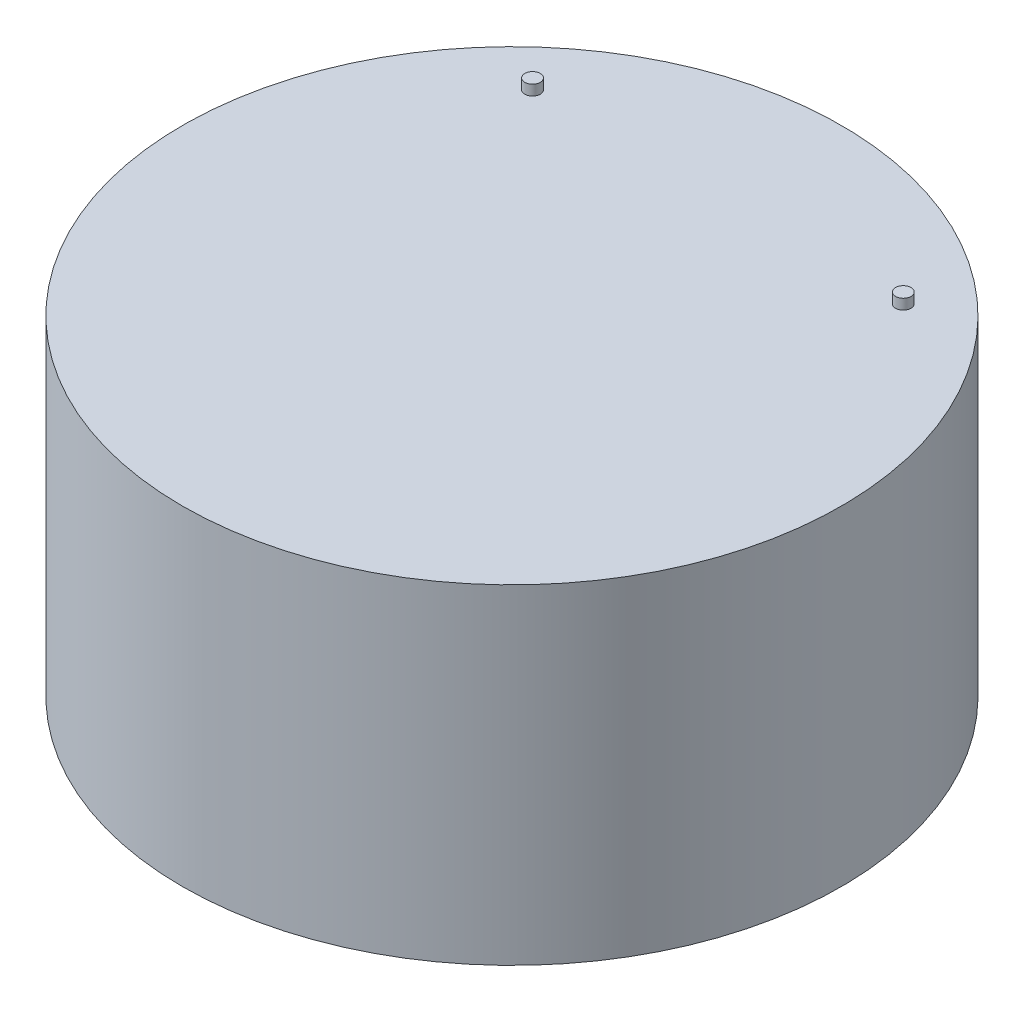
SolidWorks part; units mm, degrees
ref_plane "Front" through (0, 0, 0) normal (0, 0, 1) x (1, 0, 0)
ref_plane "Top" through (0, 0, 0) normal (0, 1, 0) x (1, 0, 0)
ref_plane "Right" through (0, 0, 0) normal (1, 0, 0) x (0, 0, -1)
sketch "Sketch1" plane through (0, 0, 0) normal (0, 1, 0) x (1, 0, 0)
  circle A0 centre (0, 0) radius 50.8
  dimension "D1" = 101.6
extrude "Boss-Extrude1" add sketch "Sketch1" along normal blind 50.8
sketch "Sketch3" plane through (0, 50.8, 0) normal (0, 1, 0) x (1, 0, 0)
  line L0 (0, 50.8) -> (0, -50.8) construction
  line L1 (28.575, 31.75) -> (39.6557, 31.75) construction
  line L2 (39.6557, 31.75) -> (-39.6557, 31.75) construction
  circle A0 centre (0, 0) radius 50.8 construction
  circle A1 centre (28.575, 31.75) radius 1.1906
  circle A2 centre (-28.575, 31.75) radius 1.1906
  dimension "D1" = 28.575
  dimension "D2" = 19.05
  dimension "D3" = 79.3115
extrude "Boss-Extrude3" add sketch "Sketch3" along normal blind 1.5883
